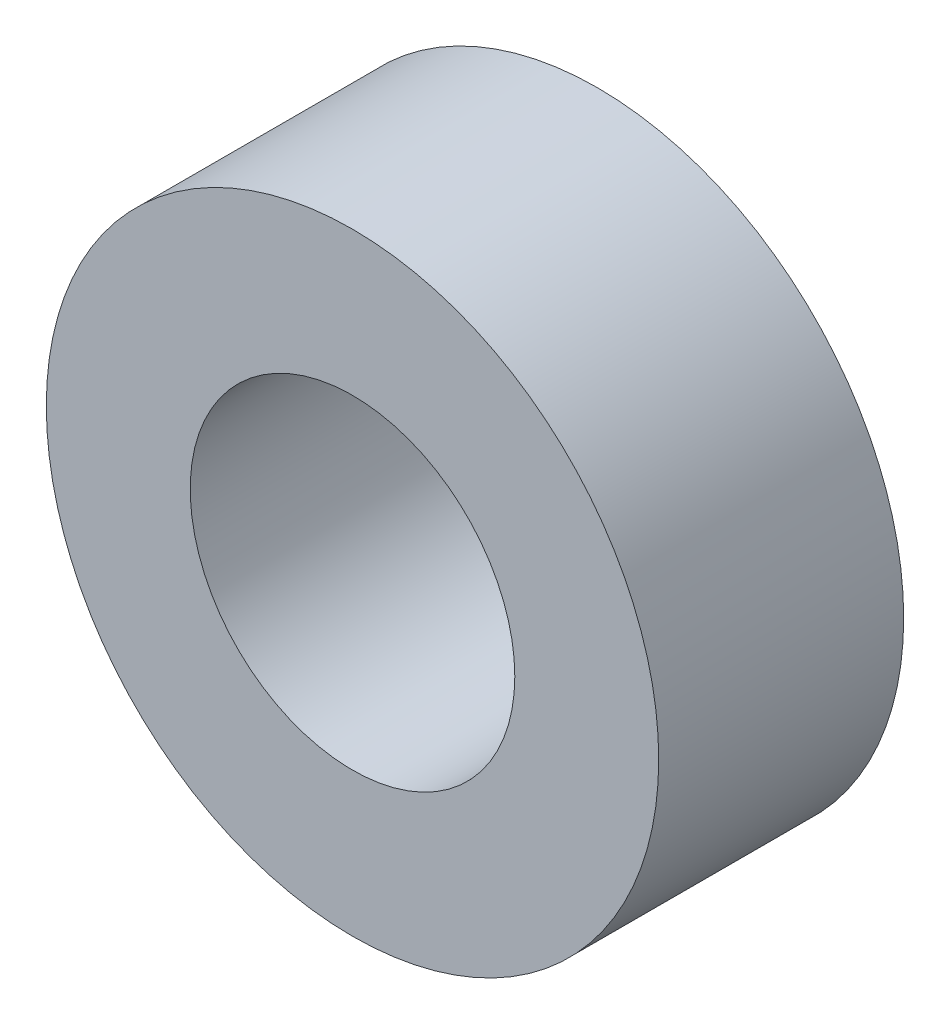
SolidWorks part; units mm, degrees
ref_plane "Front Plane" through (0, 0, 0) normal (0, 0, 1) x (1, 0, 0)
ref_plane "Top Plane" through (0, 0, 0) normal (0, 1, 0) x (1, 0, 0)
ref_plane "Right Plane" through (0, 0, 0) normal (1, 0, 0) x (0, 0, -1)
sketch "Sketch1" plane through (0, 0, 0) normal (0, 0, 1) x (1, 0, 0)
  circle A0 centre (0, 0) radius 5
  circle A1 centre (0, 0) radius 2.65
  dimension "OD" = 10
  dimension "ID" = 5.3
extrude "Extrude1" add sketch "Sketch1" along normal mid plane 4
sketch "Sketch2" plane through (0, 0, 0) normal (1, 0, 0) x (0, 0, -1)
  line L0 (-2, -2.65) -> (2, -2.65) construction
  line L3 (2, 2.65) -> (-2, 2.65) construction
  line L5 (-2, -2.65) -> (2, -2.65)
  line L6 (2, 2.65) -> (-2, 2.65)
sketch "Sketch4" plane through (0, 0, 2) normal (0, 0, 1) x (1, 0, 0)
  line L0 (0, 0) -> (-1.8738, 1.8738)
  line L1 (0, -1.1) -> (0, 1.1) construction
  circle A0 centre (0, 0) radius 2.65 construction
  dimension "D1" = 45
